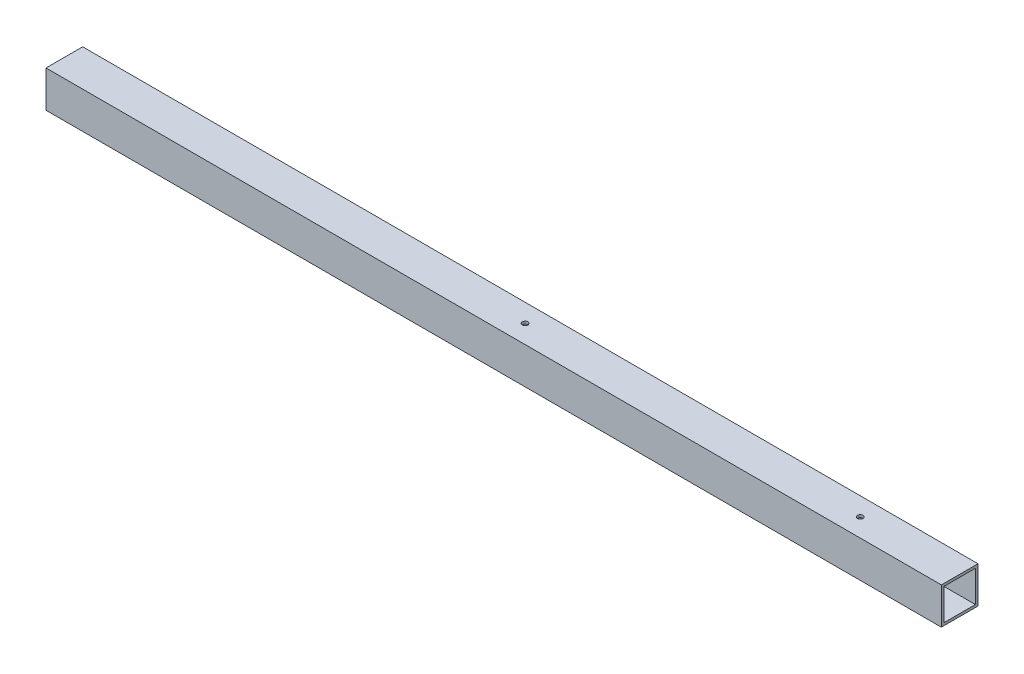
SolidWorks part; units mm, degrees
ref_plane "Front Plane" through (0, 0, 0) normal (0, 0, 1) x (1, 0, 0)
ref_plane "Top Plane" through (0, 0, 0) normal (0, 1, 0) x (1, 0, 0)
ref_plane "Right Plane" through (0, 0, 0) normal (1, 0, 0) x (0, 0, -1)
sketch "Sketch1" plane through (0, 0, 0) normal (0, 0, 1) x (1, 0, 0)
  line L1 (0, 0) -> (1085.85, 0)
  line L2 (0, 0) -> (0, 44.45)
  line L3 (0, 44.45) -> (1085.85, 44.45)
  line L4 (1085.85, 0) -> (1085.85, 44.45)
  dimension "D1" = 1085.85
  dimension "D2" = 44.45
extrude "Boss-Extrude1" add sketch "Sketch1" along normal blind 44.45
shell "Shell1" thickness 3.175
hole_wizard "H (0.266) Diameter Hole1" positions "Sketch2" profile "Sketch3" hole size "H" standard "ANSI Inch" end condition through all
sketch "Sketch2" plane through (0, 44.45, 0) normal (0, 1, 0) x (1, 0, 0)
  line L0 (1085.85, 0) -> (0, 0) construction
  point P0 (965.2, -22.225)
  point P2 (558.8, -22.225)
  dimension "D1" = 558.8
  dimension "D2" = 965.2
  dimension "D3" = 22.225
sketch "Sketch3" plane through (965.2, 44.45, 22.225) normal (1, 0, 0) x (0, 0, 1)
  line L0 (0, 0) -> (0, 44.45)
  line L1 (0, 44.45) -> (3.3782, 44.45)
  line L2 (3.3782, 44.45) -> (3.3782, 0)
  line L5 (3.3782, 0) -> (0, 0)
  line L11 (0, -6.35) -> (0, 107.95) construction
  dimension "Thru Hole Dia." = 6.7564
  dimension "Thru Hole Depth" = 44.45
